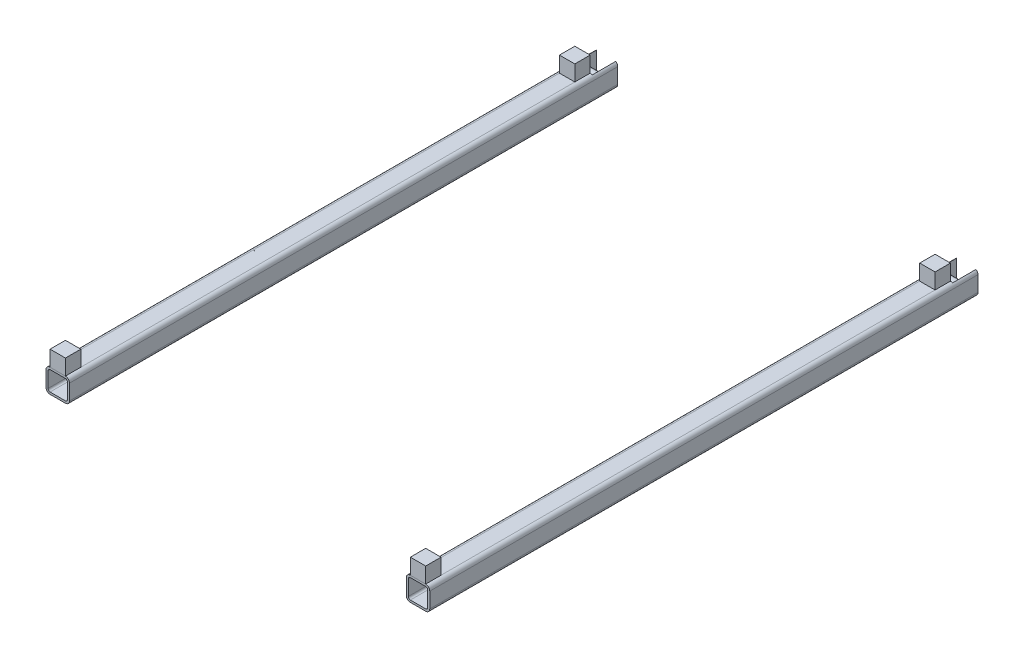
SolidWorks part; units mm, degrees
ref_plane "Front Plane" through (0, 0, 0) normal (0, 0, 1) x (1, 0, 0)
ref_plane "Top Plane" through (0, 0, 0) normal (0, 1, 0) x (1, 0, 0)
ref_plane "Right Plane" through (0, 0, 0) normal (1, 0, 0) x (0, 0, -1)
sketch "Sketch1" plane through (0, 0, 0) normal (0, 1, 0) x (1, 0, 0)
  line L2 (-230, 350) -> (-230, -350)
  line L4 (230, 350) -> (230, -350)
  line L5 (0, 350) -> (0, -186.8728) construction
  point P0 (0, 0)
  dimension "D1" = 460
  dimension "D2" = 700
other "Square tube - configured 30 X 30 X 2.6(4)"
ref_plane "Plane2" through (-230, 0, -350) normal (0, 0, 1) x (0, 1, 0)
sketch "Sketch116" plane through (-230, 0, -350) normal (0, 0, 1) x (0, 1, 0)
  line L0 (-9.8, -12.4) -> (9.8, -12.4)
  line L1 (-12.4, -9.8) -> (-12.4, 9.8)
  line L2 (9.8, 12.4) -> (-9.8, 12.4)
  line L3 (12.4, 9.8) -> (12.4, -9.8)
  line L4 (-9.8, -15) -> (9.8, -15)
  line L5 (-15, -9.8) -> (-15, 9.8)
  line L6 (9.8, 15) -> (-9.8, 15)
  line L7 (15, 9.8) -> (15, -9.8)
  arc A0 (15, 9.8) -> (9.8, 15) centre (9.8, 9.8) ccw
  arc A1 (9.8, -15) -> (15, -9.8) centre (9.8, -9.8) ccw
  arc A2 (-15, -9.8) -> (-9.8, -15) centre (-9.8, -9.8) ccw
  arc A3 (-9.8, 15) -> (-15, 9.8) centre (-9.8, 9.8) ccw
  arc A4 (-9.8, 12.4) -> (-12.4, 9.8) centre (-9.8, 9.8) ccw
  arc A5 (12.4, 9.8) -> (9.8, 12.4) centre (9.8, 9.8) ccw
  arc A6 (9.8, -12.4) -> (12.4, -9.8) centre (9.8, -9.8) ccw
  arc A7 (-12.4, -9.8) -> (-9.8, -12.4) centre (-9.8, -9.8) ccw
  point P0 (-15, 0)
  point P1 (15, 0)
  point P2 (0, 15)
  point P3 (0, -15)
  point P4 (0, 0)
  point P5 (-15, -15)
  point P6 (15, -15)
  point P7 (15, 15)
  point P8 (-15, 15)
  point P33 (0, 0)
  dimension "D1" = 5.2
  dimension "Thickness" = 2.6
  dimension "V_leg" = 30
sketch "Sketch113" plane through (0, 15, 0) normal (0, 1, 0) x (1, 0, 0)
  line L1 (-242.4, 350) -> (-217.6, 350)
  line L2 (-242.4, 350) -> (-242.4, 320)
  line L3 (-242.4, 320) -> (-217.6, 320)
  line L4 (-217.6, 350) -> (-217.6, 320)
  line L5 (-217.6, -350) -> (-217.6, 350) construction
  line L6 (0, 0) -> (0, 513.6069) construction
  line L11 (-242.4, -350) -> (-242.4, 350) construction
  line L12 (-239.8, 350) -> (-245, 350) construction
  dimension "D1" = 30
extrude "Cut-Extrude1" cut sketch "Sketch113" against normal through all
sketch "Sketch114" plane through (-217.6, 0, 0) normal (-1, 0, 0) x (0, 0, 1)
  line L0 (-350, 15) -> (-320, -15) construction
  circle A0 centre (-335, 0) radius 5
  dimension "D1" = 10
extrude "Boss-Extrude1" add sketch "Sketch114" along normal up to next separate body
sketch "Sketch115" plane through (0, 15, 0) normal (0, 1, 0) x (1, 0, 0)
  line L0 (242.4, -350) -> (242.4, 350) construction
  line L1 (217.6, 350) -> (242.4, 350)
  line L2 (217.6, 350) -> (217.6, 320)
  line L3 (217.6, 320) -> (242.4, 320)
  line L4 (242.4, 350) -> (242.4, 320)
  dimension "D1" = 30
extrude "Cut-Extrude2" cut sketch "Sketch115" against normal through all contours L2 L3 L4 L1
mirror "Mirror8" about plane through (0, 0, 0) normal (1, 0, 0) of bodies 117
sketch "Sketch117" plane through (0, 15, 0) normal (0, 1, 0) x (1, 0, 0)
  line L0 (-239.8, -350) -> (-239.8, 320) construction
  line L1 (-220.2, -350) -> (-220.2, 320) construction
  line L2 (-220.2, -350) -> (-239.8, -350) construction
  line L3 (-245, -350) -> (-239.8, -350) construction
  line L4 (-239.8, -350) -> (-220.2, -350)
  line L5 (-239.8, -350) -> (-239.8, -330.4)
  line L6 (-239.8, -330.4) -> (-220.2, -330.4)
  line L7 (-220.2, -350) -> (-220.2, -330.4)
  line L8 (-239.8, -350) -> (-220.2, -330.4) construction
  line L9 (-239.8, -330.4) -> (-220.2, -350) construction
  circle A0 centre (-230, -340.2) radius 9.8 construction
extrude "Boss-Extrude2" add sketch "Sketch117" along normal blind 20 separate body
mirror "Mirror9" about plane through (0, 0, 0) normal (1, 0, 0) of bodies 122
sketch "Sketch118" plane through (0, 15, 0) normal (0, 1, 0) x (1, 0, 0)
  line L0 (-239.8, 320) -> (-220.2, 320) construction
  line L1 (-220.2, -350) -> (-220.2, 320) construction
  line L3 (-239.8, -350) -> (-239.8, 320) construction
  line L5 (-220.2, 300.4) -> (-239.8, 300.4)
  line L6 (-220.2, 300.4) -> (-220.2, 320)
  line L7 (-220.2, 320) -> (-239.8, 320)
  line L8 (-239.8, 300.4) -> (-239.8, 320)
  line L9 (-220.2, 300.4) -> (-239.8, 320) construction
  line L10 (-220.2, 320) -> (-239.8, 300.4) construction
  circle A0 centre (-230, 310.2) radius 9.8 construction
extrude "Boss-Extrude3" add sketch "Sketch118" along normal blind 20 separate body
mirror "Mirror10" about plane through (0, 0, 0) normal (1, 0, 0) of bodies 124
